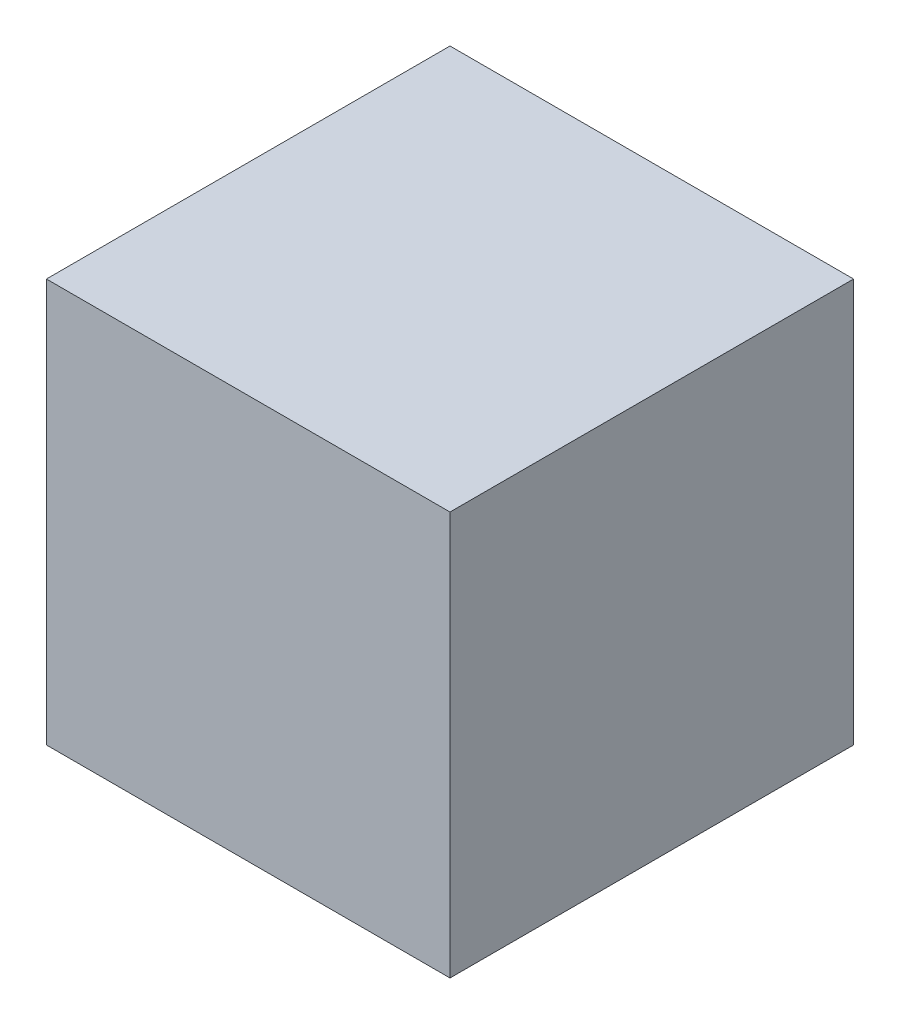
SolidWorks part; units mm, degrees
ref_plane "前视基准面" through (0, 0, 0) normal (0, 0, 1) x (1, 0, 0)
ref_plane "上视基准面" through (0, 0, 0) normal (0, 1, 0) x (1, 0, 0)
ref_plane "右视基准面" through (0, 0, 0) normal (1, 0, 0) x (0, 0, -1)
sketch "草图1" plane through (0, 0, 0) normal (0, 1, 0) x (1, 0, 0)
  line L1 (-12.7, -12.7) -> (12.7, -12.7)
  line L2 (-12.7, -12.7) -> (-12.7, 12.7)
  line L3 (-12.7, 12.7) -> (12.7, 12.7)
  line L4 (12.7, -12.7) -> (12.7, 12.7)
  line L5 (-12.7, -12.7) -> (12.7, 12.7) construction
  line L6 (-12.7, 12.7) -> (12.7, -12.7) construction
  point P0 (0, 0)
  dimension "D1" = 25.4
  dimension "D2" = 25.4
extrude "凸台-拉伸1" add sketch "草图1" along normal blind 25.4
